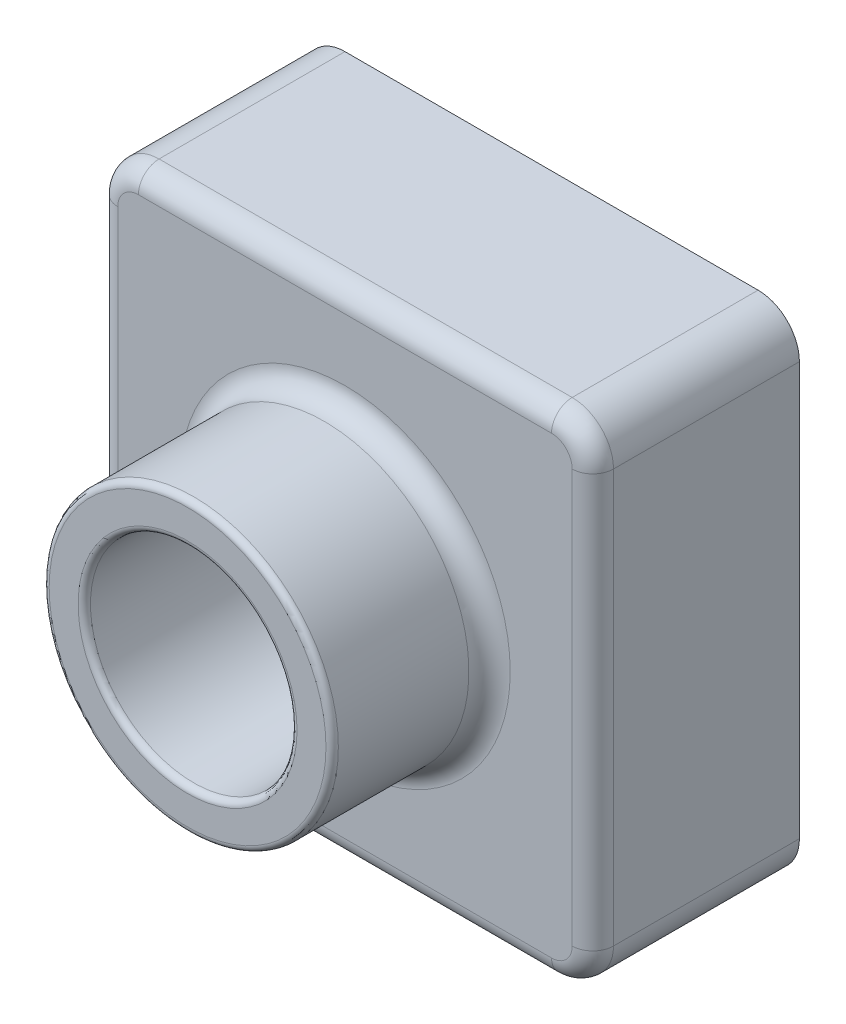
SolidWorks part; units mm, degrees
ref_plane "Front Plane" through (0, 0, 0) normal (0, 0, 1) x (1, 0, 0)
ref_plane "Top Plane" through (0, 0, 0) normal (0, 1, 0) x (1, 0, 0)
ref_plane "Right Plane" through (0, 0, 0) normal (1, 0, 0) x (0, 0, -1)
sketch "Sketch1" plane through (0, 0, 0) normal (0, 0, 1) x (1, 0, 0)
  line L1 (0, 0) -> (120, 0)
  line L2 (0, 0) -> (0, 120)
  line L3 (0, 120) -> (120, 120)
  line L4 (120, 0) -> (120, 120)
  dimension "D1" = 120
  dimension "D2" = 120
extrude "Boss-Extrude1" add sketch "Sketch1" along normal blind 50
sketch "Sketch2" plane through (0, 0, 50) normal (0, 0, 1) x (1, 0, 0)
  circle A0 centre (60, 60) radius 35
  dimension "D1" = 70
  dimension "D2" = 60
  dimension "D3" = 60
extrude "Boss-Extrude2" add sketch "Sketch2" along normal blind 38.1
sketch "Sketch6" plane through (0, 0, 88.1) normal (0, 0, 1) x (1, 0, 0)
  circle A0 centre (60, 60) radius 25
  dimension "D1" = 50
extrude "Boss-Extrude6" add sketch "Sketch6" against normal through all
sketch "Sketch7" plane through (0, 0, 88.1) normal (0, 0, 1) x (1, 0, 0)
  circle A0 centre (60, 60) radius 25
  dimension "D1" = 50
extrude "Boss-Extrude7" add sketch "Sketch7" against normal through all
sketch "Sketch8" plane through (0, 0, 88.1) normal (0, 0, 1) x (1, 0, 0)
  circle A0 centre (60, 60) radius 25
  dimension "D1" = 50
extrude "Cut-Extrude1" cut sketch "Sketch8" against normal through all
fillet "Fillet1" radius 10 4 edges at (0, 0, 25) (0, 120, 25) (120, 0, 25) (120, 120, 25)
fillet "Fillet2" radius 1.5 2 edges at (95, 60, 88.1) (85, 60, 88.1)
fillet "Fillet3" radius 5 9 edges at (2.9289, 117.0711, 50) (60, 120, 50) (117.0711, 117.0711, 50) (120, 60, 50) (117.0711, 2.9289, 50) (60, 0, 50) (2.9289, 2.9289, 50) (0, 60, 50) (95, 60, 50)
shell "Shell2" thickness 2
